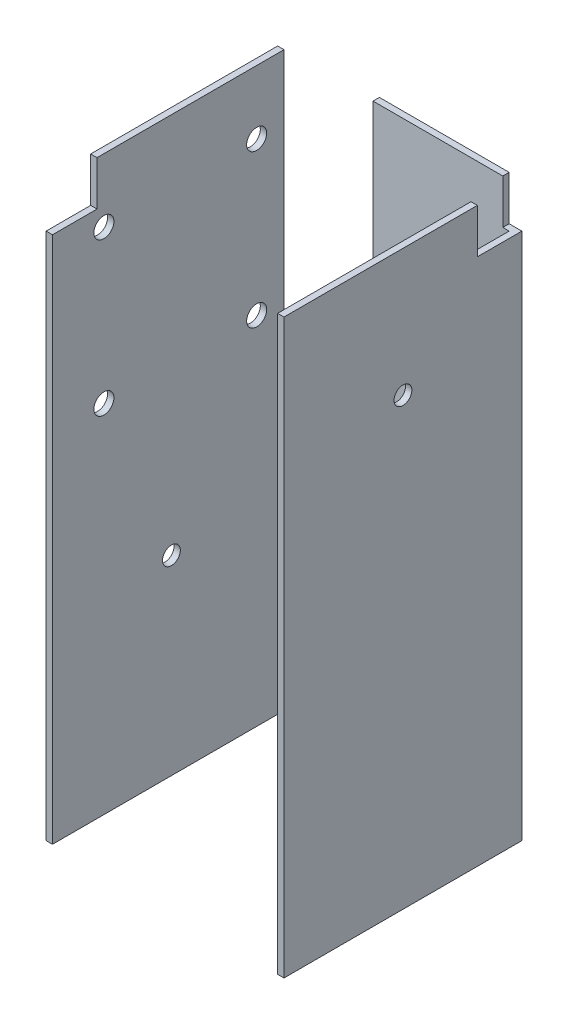
SolidWorks part; units mm, degrees
ref_plane "Front Plane" through (0, 0, 0) normal (0, 0, 1) x (1, 0, 0)
ref_plane "Top Plane" through (0, 0, 0) normal (0, 1, 0) x (1, 0, 0)
ref_plane "Right Plane" through (0, 0, 0) normal (1, 0, 0) x (0, 0, -1)
sketch "Sketch1" plane through (0, 0, 0) normal (0, 1, 0) x (1, 0, 0)
  line L1 (-23.749, 23.749) -> (23.749, 23.749)
  line L2 (-23.749, 23.749) -> (-23.749, -23.749)
  line L3 (-23.749, -23.749) -> (23.749, -23.749)
  line L4 (23.749, 23.749) -> (23.749, -23.749)
  line L5 (-22.479, -23.749) -> (22.479, -23.749)
  line L6 (-22.479, -23.749) -> (-22.479, 22.479)
  line L7 (-22.479, 22.479) -> (22.479, 22.479)
  line L8 (22.479, -23.749) -> (22.479, 22.479)
  point P4 (-23.749, 0)
  point P5 (0, -23.749)
  dimension "D1" = 47.498
  dimension "D2" = 47.498
  dimension "D3" = 1.27
  dimension "D4" = 1.27
  dimension "D5" = 1.27
extrude "Boss-Extrude1" add sketch "Sketch1" along normal blind 114.3 contours L8 L3 L4 L1 L2 L6 L7
sketch "Sketch3" plane through (22.479, 0, 0) normal (-1, 0, 0) x (0, 0, 1)
  line L0 (-23.749, 0) -> (23.749, 0) construction
  line L1 (-8.3232, 70.08) -> (21.6768, 70.08)
  line L2 (-8.3232, 70.08) -> (-8.3232, 5.08)
  line L3 (-8.3232, 5.08) -> (21.6768, 5.08)
  line L4 (21.6768, 70.08) -> (21.6768, 5.08)
  dimension "D1" = 30
  dimension "D2" = 65
  dimension "D3" = 5.08
extrude "Boss-Extrude3" [suppressed] add sketch "Sketch3" along normal blind 12.7
sketch "Sketch5" plane through (-22.479, 0, 0) normal (1, 0, 0) x (0, 0, -1)
  line L0 (23.749, 114.3) -> (-23.749, 114.3) construction
  line L1 (-20.3654, 109.22) -> (17.7346, 109.22)
  line L2 (-20.3654, 109.22) -> (-20.3654, 71.12)
  line L3 (-20.3654, 71.12) -> (17.7346, 71.12)
  line L4 (17.7346, 109.22) -> (17.7346, 71.12)
  dimension "D1" = 38.1
  dimension "D2" = 38.1
  dimension "D3" = 5.08
extrude "Boss-Extrude4" [suppressed] add sketch "Sketch5" along normal blind 19.05
sketch "Sketch8" plane through (0, 0, -23.749) normal (0, 0, -1) x (-1, 0, 0)
  line L0 (23.749, 0) -> (-23.749, 0) construction
  circle A0 centre (0, 57.15) radius 1.778
  dimension "D1" = 3.556
  dimension "D2" = 57.15
extrude "Cut-Extrude1" cut sketch "Sketch8" against normal blind 5.08
sketch "Sketch9" plane through (-23.749, 0, 0) normal (-1, 0, 0) x (0, 0, 1)
  line L0 (-23.749, 0) -> (23.749, 0) construction
  circle A0 centre (0, 38.1) radius 1.778
  dimension "D1" = 3.556
  dimension "D2" = 38.1
extrude "Cut-Extrude2" cut sketch "Sketch9" against normal blind 5.08
sketch "Sketch10" plane through (23.749, 0, 0) normal (1, 0, 0) x (0, 0, -1)
  line L0 (23.749, 114.3) -> (-23.749, 114.3) construction
  circle A0 centre (0, 88.9) radius 1.778
  dimension "D1" = 3.556
  dimension "D2" = 25.4
extrude "Cut-Extrude3" cut sketch "Sketch10" against normal blind 5.08
sketch "Sketch13" plane through (0, 0, -23.749) normal (0, 0, -1) x (-1, 0, 0)
  line L0 (23.749, 0) -> (-23.749, 0) construction
  circle A0 centre (0, 25.4) radius 1.778
  dimension "D1" = 3.556
  dimension "D2" = 25.4
extrude "Cut-Extrude6" cut sketch "Sketch13" against normal blind 5.08
sketch "Sketch14" plane through (-23.749, 0, 0) normal (-1, 0, 0) x (0, 0, 1)
  line L0 (-23.749, 114.3) -> (23.749, 114.3) construction
  line L1 (-17.018, 101.6) -> (13.482, 101.6)
  line L2 (-17.018, 101.6) -> (-17.018, 71.1)
  line L3 (-17.018, 71.1) -> (13.482, 71.1)
  line L4 (13.482, 101.6) -> (13.482, 71.1)
  line L5 (-23.749, 114.3) -> (-23.749, 0) construction
  circle A0 centre (-17.018, 101.6) radius 2
  circle A1 centre (13.482, 101.6) radius 2
  circle A2 centre (13.482, 71.1) radius 2
  circle A3 centre (-17.018, 71.1) radius 2
  point P8 (-1.768, 101.6)
  dimension "D3" = 4
  dimension "D4" = 4
  dimension "D5" = 4
  dimension "D6" = 4
  dimension "D1" = 30.5
  dimension "D2" = 30.5
  dimension "D7" = 12.7
  dimension "D8" = 6.731
extrude "Cut-Extrude7" cut sketch "Sketch14" against normal blind 2.54 contours L1 A0 L2 | L2 A0 L1 | L4 A1 L1 | L1 A1 L4 | L3 A2 L4 | L4 A2 L3 | L2 A3 L3 | L3 A3 L2
sketch "Sketch16" plane through (0, 114.3, 0) normal (0, 1, 0) x (1, 0, 0)
  line L0 (-22.479, 22.479) -> (22.479, 22.479) construction
  line L1 (-23.749, 23.749) -> (-4.699, 23.749)
  line L2 (-23.749, 23.749) -> (-23.749, 22.479)
  line L3 (-23.749, 22.479) -> (-4.699, 22.479)
  line L4 (-4.699, 23.749) -> (-4.699, 22.479)
  dimension "D1" = 19.05
extrude "Cut-Extrude8" cut sketch "Sketch16" against normal blind 47.625
sketch "Sketch17" plane through (-23.749, 0, 0) normal (-1, 0, 0) x (0, 0, 1)
  line L1 (23.749, 114.3) -> (14.859, 114.3)
  line L2 (23.749, 114.3) -> (23.749, 105.41)
  line L3 (23.749, 105.41) -> (14.859, 105.41)
  line L4 (14.859, 114.3) -> (14.859, 105.41)
  dimension "D1" = 8.89
  dimension "D2" = 8.89
extrude "Cut-Extrude9" cut sketch "Sketch17" against normal blind 38.1
sketch "Sketch18" plane through (23.749, 0, 0) normal (1, 0, 0) x (0, 0, -1)
  line L1 (23.749, 114.3) -> (14.859, 114.3)
  line L2 (23.749, 114.3) -> (23.749, 105.41)
  line L3 (23.749, 105.41) -> (14.859, 105.41)
  line L4 (14.859, 114.3) -> (14.859, 105.41)
  dimension "D1" = 8.89
  dimension "D2" = 8.89
extrude "Cut-Extrude10" cut sketch "Sketch18" against normal blind 2.54
